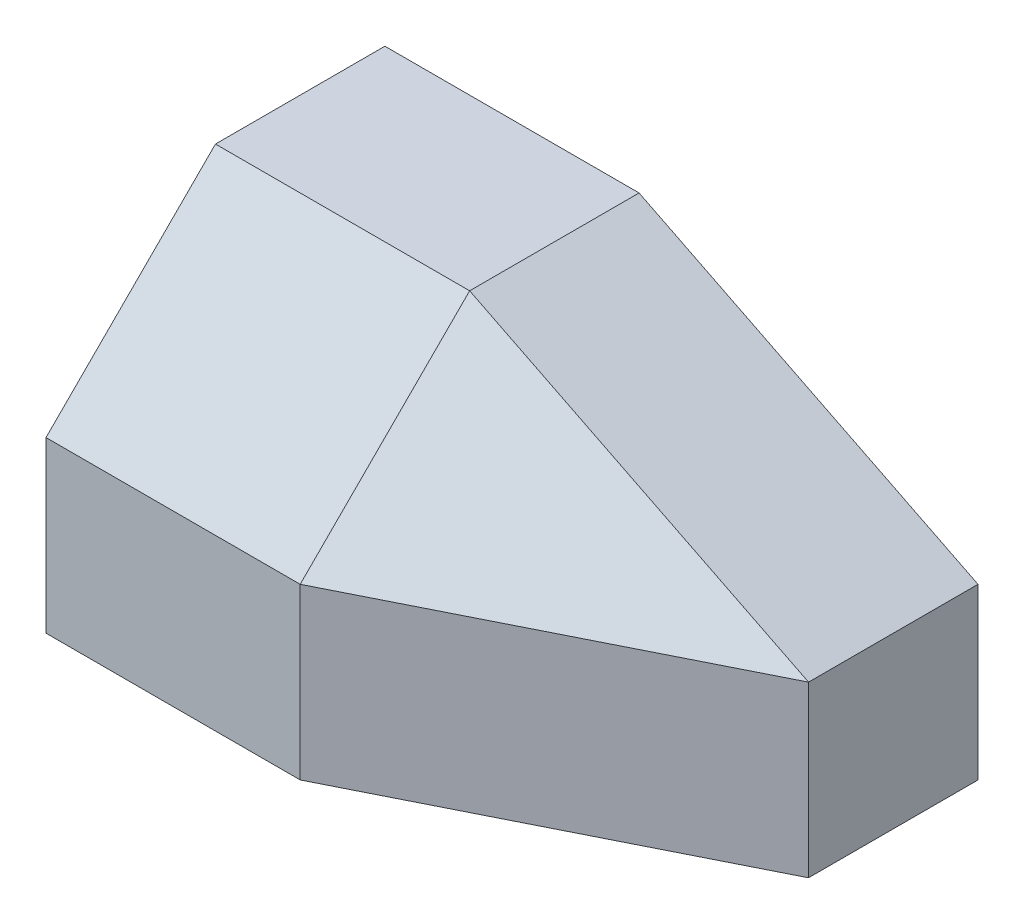
SolidWorks part; units mm, degrees
ref_plane "Front Plane" through (0, 0, 0) normal (0, 0, 1) x (1, 0, 0)
ref_plane "Top Plane" through (0, 0, 0) normal (0, 1, 0) x (1, 0, 0)
ref_plane "Right Plane" through (0, 0, 0) normal (1, 0, 0) x (0, 0, -1)
sketch "Sketch1" plane through (0, 0, 0) normal (0, 1, 0) x (1, 0, 0)
  line L0 (0, 0) -> (0, 1016)
  line L1 (0, 1016) -> (1778, 1016)
  line L2 (1778, 1016) -> (1778, 508)
  line L3 (1778, 508) -> (762, 0)
  line L4 (762, 0) -> (0, 0)
  point P3 (0, 508)
  dimension "D1" = 1778
  dimension "D2" = 1016
  dimension "D3" = 1016
extrude "Boss-Extrude1" add sketch "Sketch1" along normal blind 1016
sketch "Sketch2" plane through (0, 0, -1016) normal (0, 0, -1) x (-1, 0, 0)
  line L0 (-762, 1016) -> (-1778, 508)
  line L1 (-1778, 1016) -> (0, 1016) construction
  line L2 (-1778, 1016) -> (-1778, 0) construction
  line L3 (-1778, 508) -> (-1778, 1016)
  line L4 (-1778, 1016) -> (-762, 1016)
  dimension "D1" = 1016
extrude "Cut-Extrude1" cut sketch "Sketch2" against normal through all
sketch "Sketch3" plane through (0, 0, 0) normal (-1, 0, 0) x (0, 0, 1)
  line L0 (-1016, 1016) -> (0, 1016) construction
  line L1 (-508, 1016) -> (0, 508)
  line L2 (0, 1016) -> (0, 0) construction
  line L3 (-508, 1016) -> (0, 1016)
  line L4 (0, 1016) -> (0, 508)
  dimension "D1" = 508
  dimension "D2" = 45
extrude "Cut-Extrude2" cut sketch "Sketch3" against normal through all
ref_plane "Plane1" through (197.5556, 395.1111, 395.1111) normal (-0.3333, -0.6667, -0.6667) x (-0.9428, 0.2357, 0.2357)
other "SurfaceCut1"
